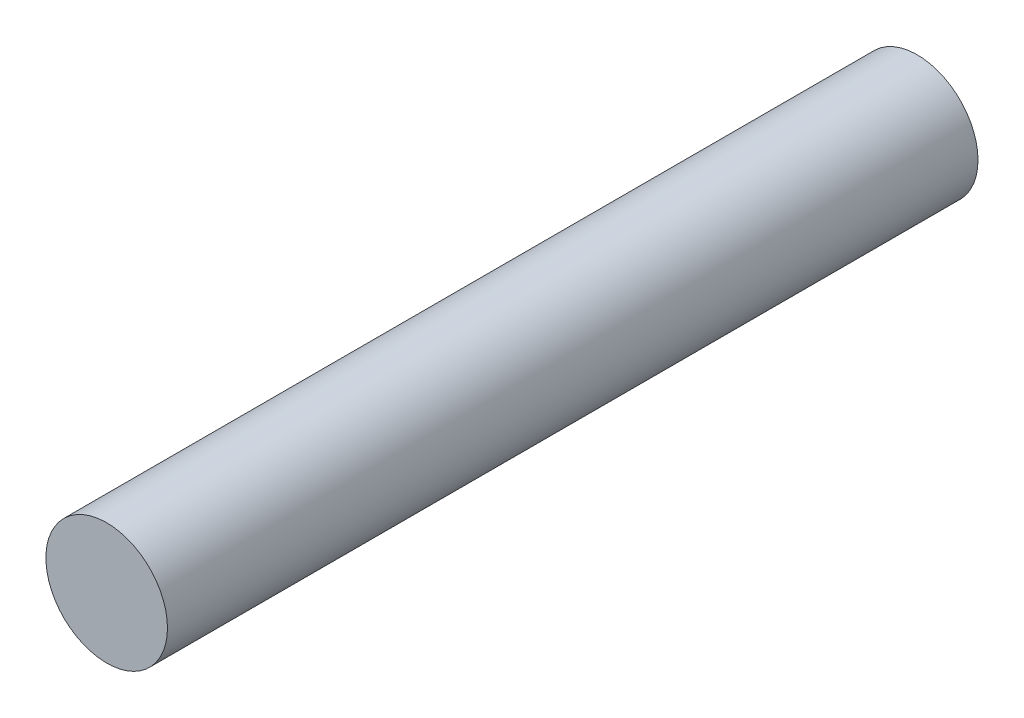
SolidWorks part; units mm, degrees
material "AISI 1045 钢，冷拔"
ref_plane "前视基准面" through (0, 0, 0) normal (0, 0, 1) x (1, 0, 0)
ref_plane "上视基准面" through (0, 0, 0) normal (0, 1, 0) x (1, 0, 0)
ref_plane "右视基准面" through (0, 0, 0) normal (1, 0, 0) x (0, 0, -1)
sketch "草图1" plane through (0, 0, 0) normal (0, 0, 1) x (1, 0, 0)
  circle A0 centre (0, 0) radius 1.5
extrude "凸台-拉伸1" add sketch "草图1" along normal blind 20
